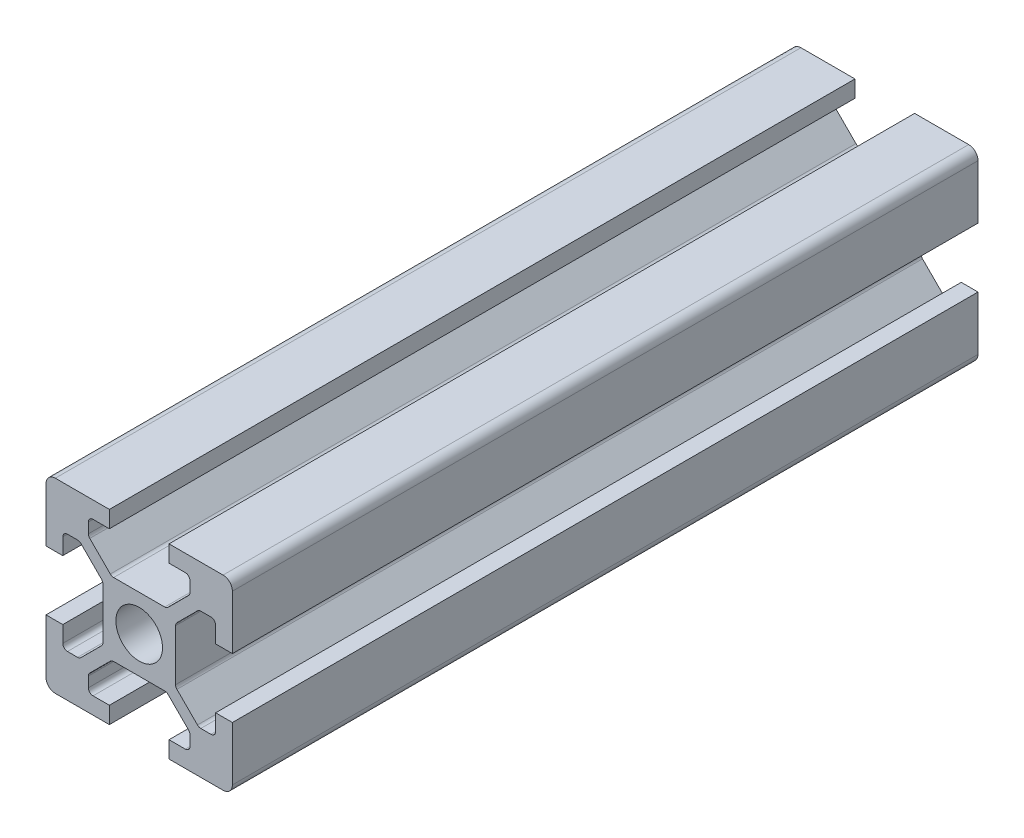
SolidWorks part; units mm, degrees
material "1060 Alloy"
ref_plane "Front Plane" through (0, 0, 0) normal (0, 0, 1) x (1, 0, 0)
ref_plane "Top Plane" through (0, 0, 0) normal (0, 1, 0) x (1, 0, 0)
ref_plane "Right Plane" through (0, 0, 0) normal (1, 0, 0) x (0, 0, -1)
sketch "Sketch1" plane through (0, 0, 0) normal (0, 0, 1) x (1, 0, 0)
  line L0 (20, 0) -> (-8.059, 28.059) construction
  line L1 (0, 0) -> (6.8, 0)
  line L2 (0, 0) -> (0, 6.8)
  line L3 (0, 20) -> (6.8, 20)
  line L4 (20, 0) -> (20, 6.8)
  line L5 (6.8, 20) -> (6.8, 18.2)
  line L6 (20, 20) -> (8.2322, 8.2322) construction
  line L7 (12.95, 6.1) -> (7.05, 6.1)
  line L8 (13.9, 7.05) -> (13.9, 12.95)
  line L9 (12.95, 13.9) -> (7.05, 13.9)
  line L10 (6.1, 7.05) -> (6.1, 12.95)
  line L11 (13.9, 6.1) -> (6.1, 13.9) construction
  line L12 (13.9, 13.9) -> (6.1, 6.1) construction
  line L13 (4.55, 16.4) -> (7.05, 13.9)
  line L14 (13.2, 18.2) -> (13.2, 20)
  line L15 (1.8, 6.8) -> (0, 6.8)
  line L16 (0, 13.2) -> (0, 20)
  line L17 (0, 13.2) -> (1.8, 13.2)
  line L18 (10, 10) -> (10, 13.9) construction
  line L19 (16.4, 4.55) -> (13.9, 7.05)
  line L20 (4.55, 16.4) -> (4.55, 18.2)
  line L21 (4.55, 18.2) -> (6.8, 18.2)
  line L22 (13.2, 18.2) -> (15.45, 18.2)
  line L23 (15.45, 18.2) -> (15.45, 16.4)
  line L24 (15.45, 16.4) -> (12.95, 13.9)
  line L25 (16.4, 4.55) -> (18.2, 4.55)
  line L26 (18.2, 4.55) -> (18.2, 6.8)
  line L27 (20, 6.8) -> (18.2, 6.8)
  line L28 (18.2, 13.2) -> (20, 13.2)
  line L29 (18.2, 13.2) -> (18.2, 15.45)
  line L30 (18.2, 15.45) -> (16.4, 15.45)
  line L31 (16.4, 15.45) -> (13.9, 12.95)
  line L32 (1.8, 4.55) -> (3.6, 4.55)
  line L33 (3.6, 15.45) -> (6.1, 12.95)
  line L34 (3.6, 15.45) -> (1.8, 15.45)
  line L35 (1.8, 15.45) -> (1.8, 13.2)
  line L36 (0, 13.2) -> (1.8, 13.2)
  line L37 (1.8, 6.8) -> (0, 6.8)
  line L38 (3.6, 4.55) -> (6.1, 7.05)
  line L39 (1.8, 6.8) -> (1.8, 4.55)
  line L40 (15.45, 3.6) -> (12.95, 6.1)
  line L41 (4.55, 3.6) -> (7.05, 6.1)
  line L42 (4.55, 1.8) -> (4.55, 3.6)
  line L43 (6.8, 1.8) -> (4.55, 1.8)
  line L44 (6.8, 1.8) -> (6.8, 0)
  line L45 (15.45, 3.6) -> (15.45, 1.8)
  line L46 (15.45, 1.8) -> (13.2, 1.8)
  line L47 (13.2, 0) -> (13.2, 1.8)
  line L48 (13.2, 20) -> (20, 20)
  line L49 (20, 13.2) -> (20, 20)
  line L50 (13.2, 0) -> (20, 0)
  line L51 (6.1, 6.1) -> (-5.5045, -5.5045) construction
  circle A0 centre (10, 10) radius 2.5
  point P25 (10, 16.4)
  point P39 (13.2, 19.1)
  point P46 (0.9, 6.8)
  dimension "D3" = 5
  dimension "D2" = 20
  dimension "D4" = 7.8
  dimension "D5" = 7.8
  dimension "D6" = 6.8
  dimension "D7" = 6.8
  dimension "D8" = 1.8
  dimension "D9" = 10.9
  dimension "D10" = 1.8
  dimension "D11" = 10.9
  dimension "D12" = 20
extrude "Boss-Extrude1" add sketch "Sketch1" along normal blind 80 contours L47 L50 L4 L27 L26 L25 L19 L8 L31 L30 L29 L28 L49 L48 L14 L22 L23 L24 L9 L13 L20 L21 L5 L3 L16 L17 L35 L34 L33 L10 L38 L32 L39 L15 L2 L1 L44 L43 L42 L41 L7 L40 L45 L46 A0
fillet "Fillet1" radius 1 4 edges at (20, 20, 40) (20, 0, 40) (0, 0, 40) (0, 20, 40)
fillet "Fillet2" radius 0.5 6 edges at (4.55, 18.2, 40) (4.55, 16.4, 40) (7.05, 13.9, 40) (15.45, 18.2, 40) (15.45, 16.4, 40) (12.95, 13.9, 40)
fillet "Fillet3" radius 0.5 6 edges at (18.2, 15.45, 40) (16.4, 15.45, 40) (13.9, 12.95, 40) (18.2, 4.55, 40) (13.9, 7.05, 40) (16.4, 4.55, 40)
fillet "Fillet4" radius 0.5 6 edges at (1.8, 15.45, 40) (3.6, 15.45, 40) (6.1, 12.95, 40) (3.6, 4.55, 40) (1.8, 4.55, 40) (6.1, 7.05, 40)
fillet "Fillet5" radius 0.5 6 edges at (7.05, 6.1, 40) (4.55, 3.6, 40) (4.55, 1.8, 40) (15.45, 1.8, 40) (15.45, 3.6, 40) (12.95, 6.1, 40)
sketch "Sketch2" plane through (0, 13.9, 0) normal (0, 1, 0) x (1, 0, 0)
  circle A0 centre (10, -58) radius 2.5
  circle A1 centre (10, -70) radius 2.5
  circle A4 centre (10, -34) radius 2.5
  circle A5 centre (10, -46) radius 2.5
  circle A6 centre (10, -22) radius 2.5
  circle A7 centre (10, -10) radius 2.5
  point P12 (0, 0)
  point P16 (0, 0)
  dimension "D1" = 12
  dimension "D4" = 12
  dimension "D2" = 12
  dimension "D3" = 12
  dimension "D5" = 12
extrude "Cut-Extrude1" cut sketch "Sketch2" against normal blind 8
